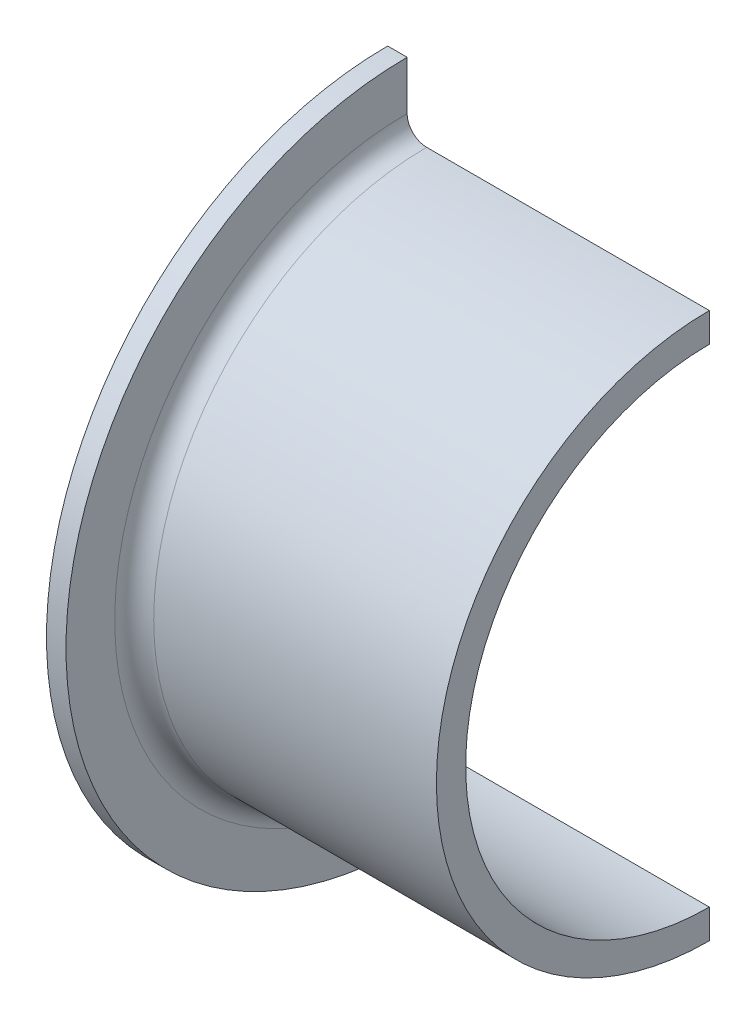
SolidWorks part; units mm, degrees
material "PE Wysoka gęstość"
ref_plane "Płaszczyzna XY" through (0, 0, 0) normal (0, 0, 1) x (1, 0, 0)
ref_plane "Płaszczyzna XZ" through (0, 0, 0) normal (0, 1, 0) x (1, 0, 0)
ref_plane "Płaszczyzna YZ" through (0, 0, 0) normal (1, 0, 0) x (0, 0, -1)
sketch "Szkic1" plane through (0, 0, 0) normal (0, 0, 1) x (1, 0, 0)
  line L0 (0, 0) -> (16.5, 0) construction
  line L1 (16.5, 12.5) -> (1, 12.5)
  line L2 (0, 13.5) -> (0, 17.5)
  line L3 (0, 17.5) -> (1, 17.5)
  line L4 (1, 17.5) -> (1, 15)
  line L5 (2, 14) -> (16.5, 14)
  line L6 (16.5, 14) -> (16.5, 12.5)
  arc A0 (1, 15) -> (2, 14) centre (2, 15) ccw
  arc A1 (1, 12.5) -> (0, 13.5) centre (1, 13.5) cw
  point P5 (0.5, 17.5)
  dimension "D5" = 1
  dimension "D1" = 12.5
  dimension "D2" = 14
  dimension "D3" = 1
  dimension "D4" = 17.5
  dimension "D6" = 16.5
revolve "Obrót1" add sketch "Szkic1" angle 180 about L0
sketch "Szkic3" plane through (16.5, 0, 0) normal (1, 0, 0) x (0, 0, -1)
  line L0 (0, 0) -> (0, 17.5) construction
  line L1 (0.75, 17.4839) -> (0.75, 12.4775)
  line L2 (-0.75, 17.4839) -> (-0.75, 12.4775)
  circle A0 centre (0, 0) radius 17.5 construction
  circle A1 centre (0, 0) radius 12.5 construction
  circle A2 centre (0, 0) radius 17.5
  circle A3 centre (0, 0) radius 12.5
  arc M4 (0, 14) -> (0, -14) centre (0, 0) ccw
  arc M5 (0, -12.5) -> (0, 12.5) centre (0, 0) cw
  dimension "D1" = 0.75
  dimension "D2" = 0.75
extrude "Wytnij-wyciągnięcie1" [suppressed] cut sketch "Szkic3" against normal through all contours L0 L1 A2 M4 | L0 A2 L2 M4 | L0 L2 M5 M4 | L0 A3 L1 M4
